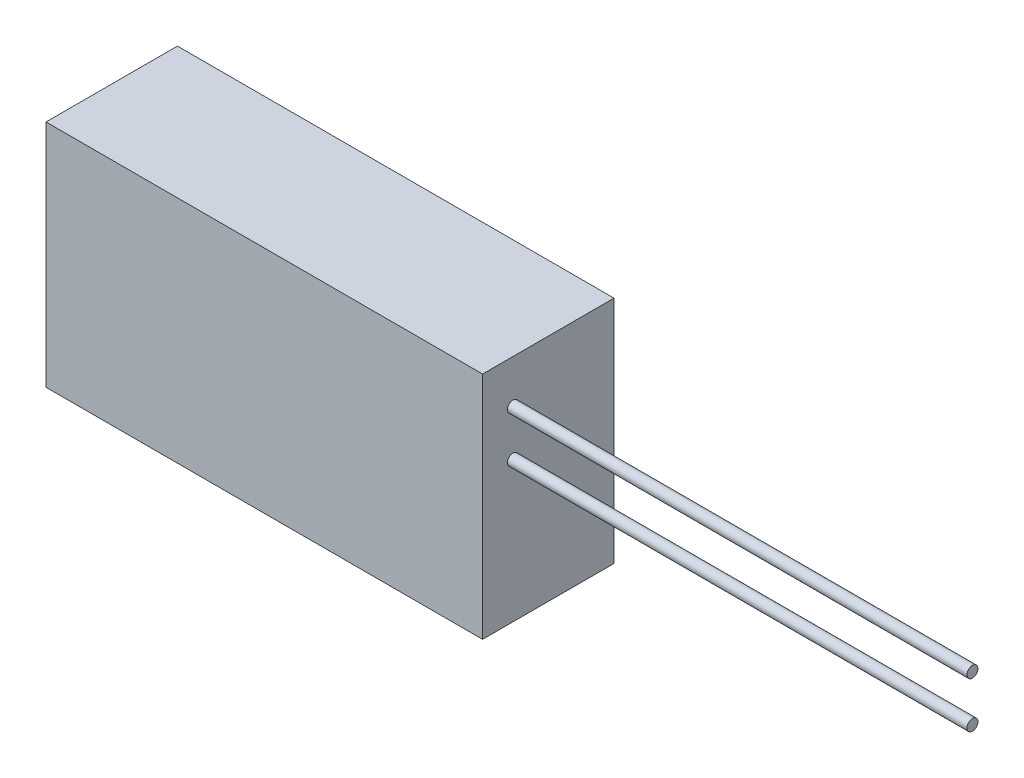
SolidWorks part; units mm, degrees
ref_plane "前基準面" through (0, 0, 0) normal (0, 0, 1) x (1, 0, 0)
ref_plane "上基準面" through (0, 0, 0) normal (0, 1, 0) x (1, 0, 0)
ref_plane "右基準面" through (0, 0, 0) normal (1, 0, 0) x (0, 0, -1)
sketch "草圖1" plane through (0, 0, 0) normal (0, 0, 1) x (1, 0, 0)
  line L1 (23.75, -12.5) -> (-23.75, -12.5)
  line L2 (23.75, -12.5) -> (23.75, 12.5)
  line L3 (23.75, 12.5) -> (-23.75, 12.5)
  line L4 (-23.75, -12.5) -> (-23.75, 12.5)
  line L5 (23.75, -12.5) -> (-23.75, 12.5) construction
  line L6 (23.75, 12.5) -> (-23.75, -12.5) construction
  point P0 (0, 0)
  dimension "D1" = 47.5
  dimension "D2" = 25
extrude "填料-伸長1" add sketch "草圖1" along normal mid plane 14.3
sketch "草圖2" plane through (23.75, 0, 0) normal (1, 0, 0) x (0, 0, -1)
  line L0 (-7.15, -12.5) -> (-7.15, 12.5) construction
  line L1 (-7.15, 12.5) -> (7.15, 12.5) construction
  circle A0 centre (-3.85, 2.8) radius 0.6
  circle A1 centre (-3.85, 7.8) radius 0.6
  point P8 (0, 0)
  dimension "D1" = 1.2
  dimension "D2" = 5
  dimension "D3" = 3.3
  dimension "D4" = 4.7
extrude "填料-伸長2" add sketch "草圖2" along normal blind 50
